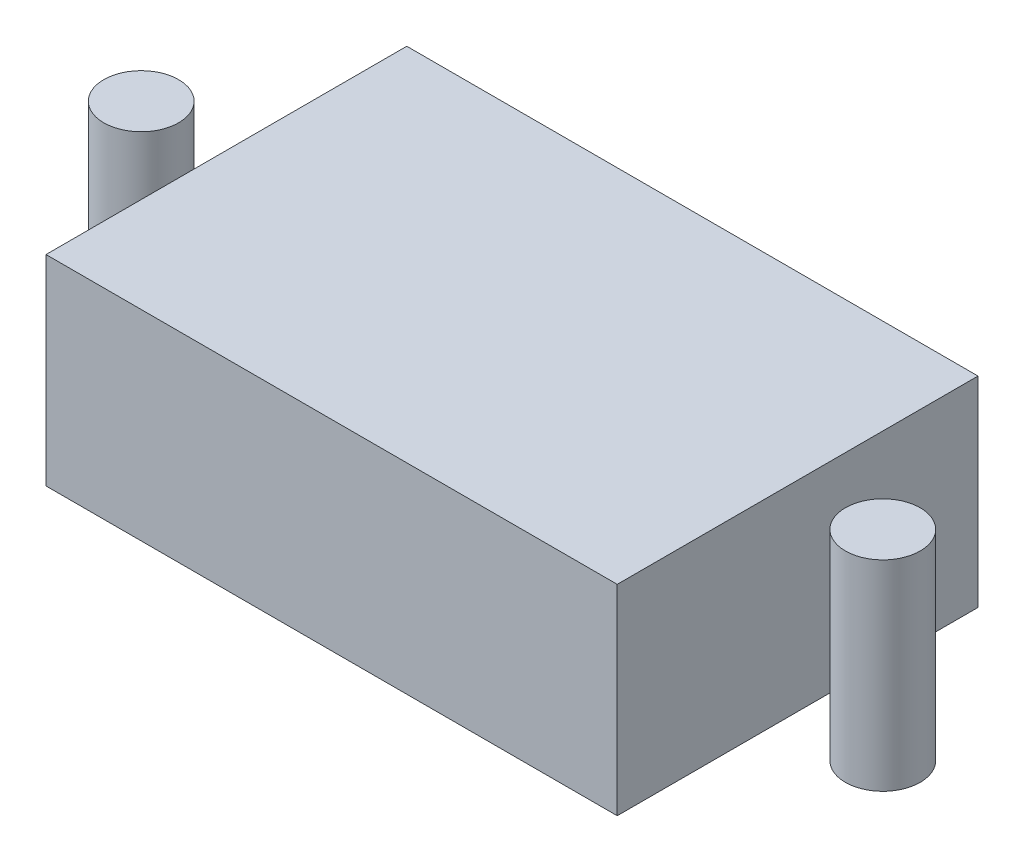
SolidWorks part; units mm, degrees
ref_plane "Front Plane" through (0, 0, 0) normal (0, 0, 1) x (1, 0, 0)
ref_plane "Top Plane" through (0, 0, 0) normal (0, 1, 0) x (1, 0, 0)
ref_plane "Right Plane" through (0, 0, 0) normal (1, 0, 0) x (0, 0, -1)
sketch "Sketch2" plane through (0, 0, 0) normal (0, 1, 0) x (1, 0, 0)
  line L1 (-14.25, -9) -> (14.25, -9)
  line L2 (-14.25, -9) -> (-14.25, 9)
  line L3 (-14.25, 9) -> (14.25, 9)
  line L4 (14.25, -9) -> (14.25, 9)
  line L5 (-14.25, -9) -> (14.25, 9) construction
  line L6 (-14.25, 9) -> (14.25, -9) construction
  circle A1 centre (18.5, 0) radius 1.8669
  circle A2 centre (-18.5, 0) radius 1.8669
  point P4 (0, 0)
extrude "Boss-Extrude1" add sketch "Sketch2" along normal blind 10
